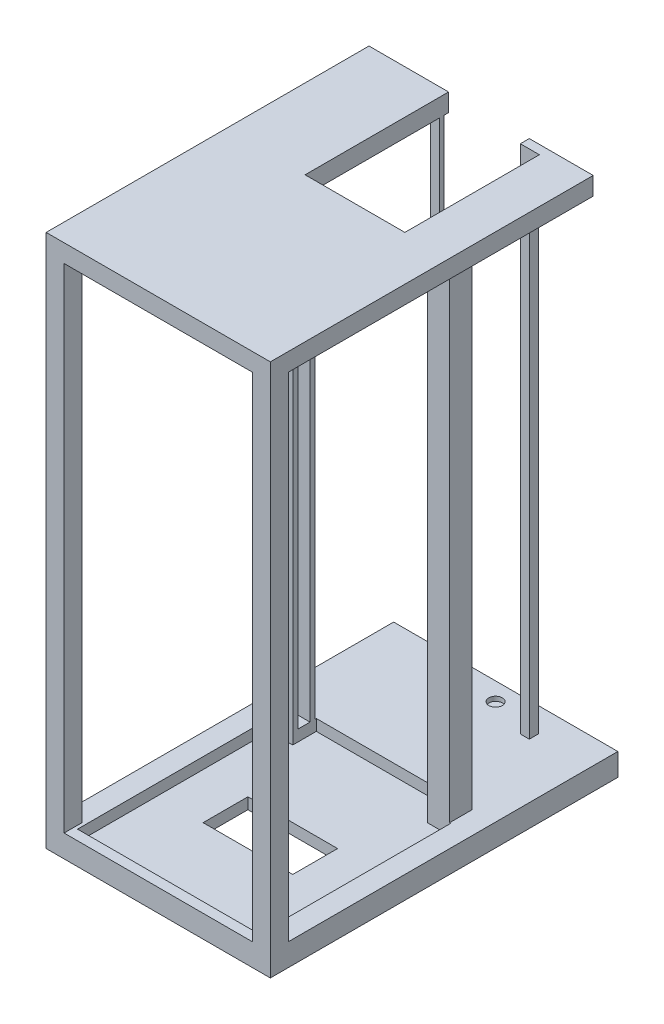
SolidWorks part; units mm, degrees
ref_plane "Front Plane" through (0, 0, 0) normal (0, 0, 1) x (1, 0, 0)
ref_plane "Top Plane" through (0, 0, 0) normal (0, 1, 0) x (1, 0, 0)
ref_plane "Right Plane" through (0, 0, 0) normal (1, 0, 0) x (0, 0, -1)
sketch "Sketch1" plane through (0, 0, 0) normal (0, 1, 0) x (1, 0, 0)
  line L1 (-50, -50) -> (50, -50)
  line L2 (-50, -50) -> (-50, 50)
  line L3 (-50, 50) -> (50, 50)
  line L4 (50, -50) -> (50, 50)
  line L5 (-50, -50) -> (50, 50) construction
  line L6 (-50, 50) -> (50, -50) construction
  line L7 (-40, -40) -> (40, -40) construction
  line L8 (-40, -40) -> (-40, 40) construction
  line L9 (-40, 40) -> (40, 40) construction
  line L10 (40, -40) -> (40, 40) construction
  line L11 (-40, -40) -> (40, 40) construction
  line L12 (-40, 40) -> (40, -40) construction
  line L13 (-20, -10) -> (20, -10) construction
  line L14 (-20, -10) -> (-20, 10) construction
  line L15 (-20, 10) -> (20, 10) construction
  line L16 (20, -10) -> (20, 10) construction
  line L17 (-20, -10) -> (20, 10) construction
  line L18 (-20, 10) -> (20, -10) construction
  point P0 (0, 0)
  point P5 (0, 0)
  point P11 (0, 0)
  dimension "D1" = 100
  dimension "D2" = 100
  dimension "D3" = 80
  dimension "D4" = 80
  dimension "D5" = 40
  dimension "D6" = 20
extrude "Boss-Extrude1" add sketch "Sketch1" along normal blind 10
sketch "Sketch2" plane through (0, 10, 0) normal (0, 1, 0) x (1, 0, 0)
  line L1 (-30, -30) -> (30, -30)
  line L2 (-30, -30) -> (-30, 30)
  line L3 (-30, 30) -> (30, 30)
  line L4 (30, -30) -> (30, 30)
  line L5 (-30, -30) -> (30, 30) construction
  line L6 (-30, 30) -> (30, -30) construction
  point P0 (0, 0)
  dimension "D1" = 60
  dimension "D2" = 60
sketch "Sketch3" plane through (0, 10, 0) normal (0, 1, 0) x (1, 0, 0)
  line L0 (-40, 40) -> (-40, 50)
  line L1 (-50, 50) -> (50, 50) construction
  line L2 (-40, 50) -> (-30, 50)
  line L3 (-30, 50) -> (-30, 47.7)
  line L4 (-30, 47.7) -> (-37, 47.7)
  line L5 (-37, 47.7) -> (-37, 42.3)
  line L6 (-37, 42.3) -> (-30, 42.3)
  line L7 (-30, 42.3) -> (-30, 40)
  line L8 (-40, 40) -> (40, 40) construction
  line L9 (-30, 40) -> (-40, 40)
  line L10 (0, 0) -> (0, 50) construction
  line L11 (30, 42.3) -> (30, 40)
  line L12 (37, 42.3) -> (30, 42.3)
  line L13 (37, 47.7) -> (37, 42.3)
  line L14 (30, 47.7) -> (37, 47.7)
  line L15 (30, 50) -> (30, 47.7)
  line L16 (40, 50) -> (30, 50)
  line L17 (40, 40) -> (40, 50)
  line L18 (30, 40) -> (40, 40)
  dimension "D1" = 2.3
  dimension "D2" = 2.3
  dimension "D3" = 10
  dimension "D4" = 10
  dimension "D5" = 3
extrude "Boss-Extrude2" add sketch "Sketch3" along normal blind 220
sketch "Sketch4" plane through (0, 0, 0) normal (0, 1, 0) x (1, 0, 0)
  line L0 (0, 30) -> (0, 90) construction
  line L1 (-50, 50) -> (50, 50)
  line L2 (-50, 50) -> (-50, 90)
  line L3 (-50, 90) -> (50, 90)
  line L4 (50, 50) -> (50, 90)
  line L5 (-30, 30) -> (30, 30) construction
  dimension "D1" = 40
  dimension "D2" = 100
  dimension "D3" = 60
extrude "Boss-Extrude3" add sketch "Sketch4" along normal blind 10
ref_plane "Plane1" through (0, 230, 0) normal (0, 1, 0) x (1, 0, 0)
sketch "Sketch5" plane through (0, 230, 0) normal (0, 1, 0) x (1, 0, 0)
  line L1 (-50, 90) -> (50, 90)
  line L2 (-50, 90) -> (-50, -50)
  line L3 (-50, -50) -> (50, -50)
  line L4 (50, 90) -> (50, -50)
extrude "Boss-Extrude4" add sketch "Sketch5" along normal blind 8
sketch "Sketch6" plane through (0, 238, 0) normal (0, 1, 0) x (1, 0, 0)
  line L0 (-40, 40) -> (40, 50) construction
  line L1 (-50, 50) -> (50, 50) construction
  line L2 (40, 50) -> (40, 40) construction
  line L3 (40, 40) -> (-40, 50) construction
  line L4 (-50, 90) -> (-41, 90) construction
  line L9 (-4.5, 45) -> (4.5, 45) construction
  line L10 (-4.5, 45) -> (-23.2, 45) construction
  line L15 (50, 90) -> (-50, 90) construction
  line L16 (-41, 90) -> (-22.3, 90) construction
  line L17 (-23.2, 45) -> (-32.2, 45) construction
  line L23 (-30, 30) -> (30, 30) construction
  line L24 (-4.5, 30) -> (30, 30)
  line L25 (-4.5, 30) -> (-4.5, 35) construction
  line L27 (30, 90) -> (-4.5, 90)
  line L30 (30, 30) -> (30, 90)
  line L31 (-4.5, 30) -> (30, 90) construction
  line L32 (-4.5, 90) -> (30, 30) construction
  line L33 (-4.5, 35) -> (-4.5, 61) construction
  line L34 (-14.5, 71) -> (-5.5, 71) construction
  line L35 (-14.5, 71) -> (-33.2, 71) construction
  line L36 (-33.2, 71) -> (-42.2, 71) construction
  line L37 (-4.5, 35) -> (-4.5, 87) construction
  line L41 (-4.5, 45) -> (25.5, 45) construction
  line L42 (25.5, 45) -> (25.5, 97) construction
  line L43 (25.5, 97) -> (-4.5, 97) construction
  line L44 (-4.5, 30) -> (-14.5, 30)
  line L45 (25.5, 97) -> (-4.5, 45) construction
  line L46 (-4.5, 45) -> (-4.5, 97) construction
  line L47 (-4.5, 97) -> (25.5, 45) construction
  line L48 (0.5, 92) -> (20.5, 92) construction
  line L49 (0.5, 92) -> (0.5, 102) construction
  line L50 (0.5, 102) -> (20.5, 102) construction
  line L51 (20.5, 92) -> (20.5, 102) construction
  line L52 (0.5, 92) -> (20.5, 102) construction
  line L53 (0.5, 102) -> (20.5, 92) construction
  line L54 (-14.5, 30) -> (-14.5, 90)
  line L55 (-14.5, 90) -> (-4.5, 90)
  point P5 (0, 45)
  point P11 (0, 45)
  point P31 (10.5, 97)
  dimension "D1" = 9
  dimension "D2" = 18.7
  dimension "D3" = 9
  dimension "D4" = 9
  dimension "D5" = 18.7
  dimension "D6" = 41
  dimension "D7" = 60
  dimension "D8" = 5
  dimension "D9" = 26
  dimension "D10" = 52
  dimension "D11" = 52
  dimension "D12" = 30
  dimension "D13" = 10
  dimension "D14" = 20
  dimension "D15" = 10
  dimension "D16" = 44.5
extrude "Cut-Extrude2" cut sketch "Sketch6" against normal blind 11
sketch "Sketch7" plane through (0, 10, 0) normal (0, 1, 0) x (1, 0, 0)
  line L0 (-50, -50) -> (50, 50) construction
  line L1 (-50, -50) -> (-42, -50)
  line L2 (-50, -50) -> (-50, -42)
  line L3 (-50, -42) -> (-42, -42)
  line L4 (-42, -50) -> (-42, -42)
  line L5 (0, 0) -> (0, -50) construction
  line L6 (-50, -50) -> (50, -50) construction
  line L7 (42, -50) -> (42, -42)
  line L8 (50, -50) -> (42, -50)
  line L9 (50, -50) -> (50, -42)
  line L10 (50, -42) -> (42, -42)
  point P12 (-46, -50)
  point P15 (46, -50)
  dimension "D1" = 8
extrude "Boss-Extrude5" add sketch "Sketch7" along normal blind 220
sketch "Sketch8" plane through (0, 10, 0) normal (0, 1, 0) x (1, 0, 0)
  line L1 (30, 40) -> (40.5, 40)
  line L2 (40, 40) -> (40, -40) construction
  line L7 (-40, 40) -> (40, 40) construction
  line L8 (-30, 40) -> (-30, 50.5)
  line L10 (30, 40) -> (30, 50.5)
  line L14 (-40.5, 40) -> (-30, 40)
  line L15 (-40.5, -40) -> (40.5, 40) construction
  line L16 (-40.5, 40) -> (40.5, -40) construction
  line L17 (-30, 50.5) -> (30, 50.5)
  line L18 (40.5, 40) -> (40.5, -45.5)
  line L19 (40.5, -45.5) -> (-40.5, -45.5)
  line L20 (-40.5, -45.5) -> (-40.5, 40)
  point P0 (0, 0)
  dimension "D1" = 10.5
  dimension "D2" = 10.5
  dimension "D3" = 10.5
  dimension "D4" = 85.5
  dimension "D5" = 81
extrude "Cut-Extrude3" cut sketch "Sketch8" against normal blind 5
sketch "Sketch9" plane through (0, 5, 0) normal (0, 1, 0) x (1, 0, 0)
  line L1 (-20, -10) -> (20, -10)
  line L2 (-20, -10) -> (-20, 10)
  line L3 (-20, 10) -> (20, 10)
  line L4 (20, -10) -> (20, 10)
extrude "Cut-Extrude4" cut sketch "Sketch9" against normal up to next
sketch "Sketch11" plane through (0, 0, 0) normal (0, 1, 0) x (1, 0, 0)
  line L1 (-50, 90) -> (50, 90)
  line L2 (-50, 90) -> (-50, 105)
  line L3 (-50, 105) -> (50, 105)
  line L4 (50, 90) -> (50, 105)
  dimension "D1" = 15
  dimension "D2" = 100
extrude "Boss-Extrude6" add sketch "Sketch11" along normal blind 10
sketch "Sketch12" plane through (0, 10, 0) normal (0, 1, 0) x (1, 0, 0)
  line L1 (10.5, 102) -> (10.5, 91.9356) construction
  line L2 (-16.5, 102) -> (23.5, 102) construction
  line L14 (-16.5, 91.9356) -> (23.5, 91.9356) construction
  line L15 (-16.5, 91.9356) -> (23.5, 102) construction
  line L16 (-16.5, 102) -> (23.5, 91.9356) construction
  line L17 (23.5, 91.9356) -> (23.5, 102) construction
  line L18 (-16.5, 91.9356) -> (-16.5, 102) construction
  circle A1 centre (3.5, 96.9678) radius 3 construction
  circle A2 centre (3.5, 96.9678) radius 3
  point P5 (3.5, 96.9678)
  point P18 (10.5, 96.9678)
  dimension "D2" = 6
extrude "Cut-Extrude5" cut sketch "Sketch12" against normal blind 2
sketch "Sketch13" plane through (0, 10, 0) normal (0, 1, 0) x (1, 0, 0)
  line L1 (21.5, 92) -> (23.5, 92)
  line L6 (0.5, 92) -> (20.5, 92) construction
  line L8 (10.5, 102) -> (10.5, 92) construction
  line L9 (0.5, 102) -> (20.5, 102) construction
  line L21 (-50, 105) -> (-50, -42) construction
  line L34 (-16.5, 102) -> (23.5, 102) construction
  line L35 (25.5, 94) -> (25.5, 90)
  line L36 (-14.5, 92) -> (-16.5, 92)
  line L37 (23.5, 92) -> (23.5, 94)
  line L38 (21.5, 90) -> (21.5, 92)
  line L39 (-16.5, 94) -> (-18.5, 94)
  line L40 (-18.5, 94) -> (-18.5, 90)
  line L41 (-18.5, 90) -> (-14.5, 90)
  line L42 (-14.5, 90) -> (-14.5, 92)
  line L43 (25.5, 90) -> (21.5, 90)
  line L44 (23.5, 94) -> (25.5, 94)
  line L45 (-16.5, 92) -> (-16.5, 94)
  line L46 (-16.5, 92) -> (23.5, 92) construction
  line L47 (-16.5, 92) -> (23.5, 102) construction
  line L48 (-16.5, 102) -> (23.5, 92) construction
  line L49 (23.5, 92) -> (23.5, 102) construction
  line L50 (-16.5, 92) -> (-16.5, 102) construction
  circle A1 centre (3.5, 97) radius 3 construction
  point P4 (3.5, 97)
  point P21 (10.5, 97)
  dimension "D4" = 6
  dimension "D1" = 31.5
  dimension "D2" = 33.5
  dimension "D3" = 53.5
extrude "Boss-Extrude7" add sketch "Sketch13" along normal blind 228
sketch "Sketch14" plane through (0, 238, 0) normal (0, 1, 0) x (1, 0, 0)
  line L0 (50, -42) -> (50, 105) construction
  line L1 (-50, 90) -> (-14.5, 90)
  line L2 (-50, 90) -> (-50, 94)
  line L3 (-50, 94) -> (-14.5, 94)
  line L4 (-14.5, 90) -> (-14.5, 94)
  line L5 (21.5, 90) -> (50, 90)
  line L6 (21.5, 90) -> (21.5, 94)
  line L7 (21.5, 94) -> (50, 94)
  line L8 (50, 90) -> (50, 94)
  dimension "D1" = 4
  dimension "D2" = 4
  dimension "D3" = 35.5
extrude "Boss-Extrude8" add sketch "Sketch14" against normal blind 8
